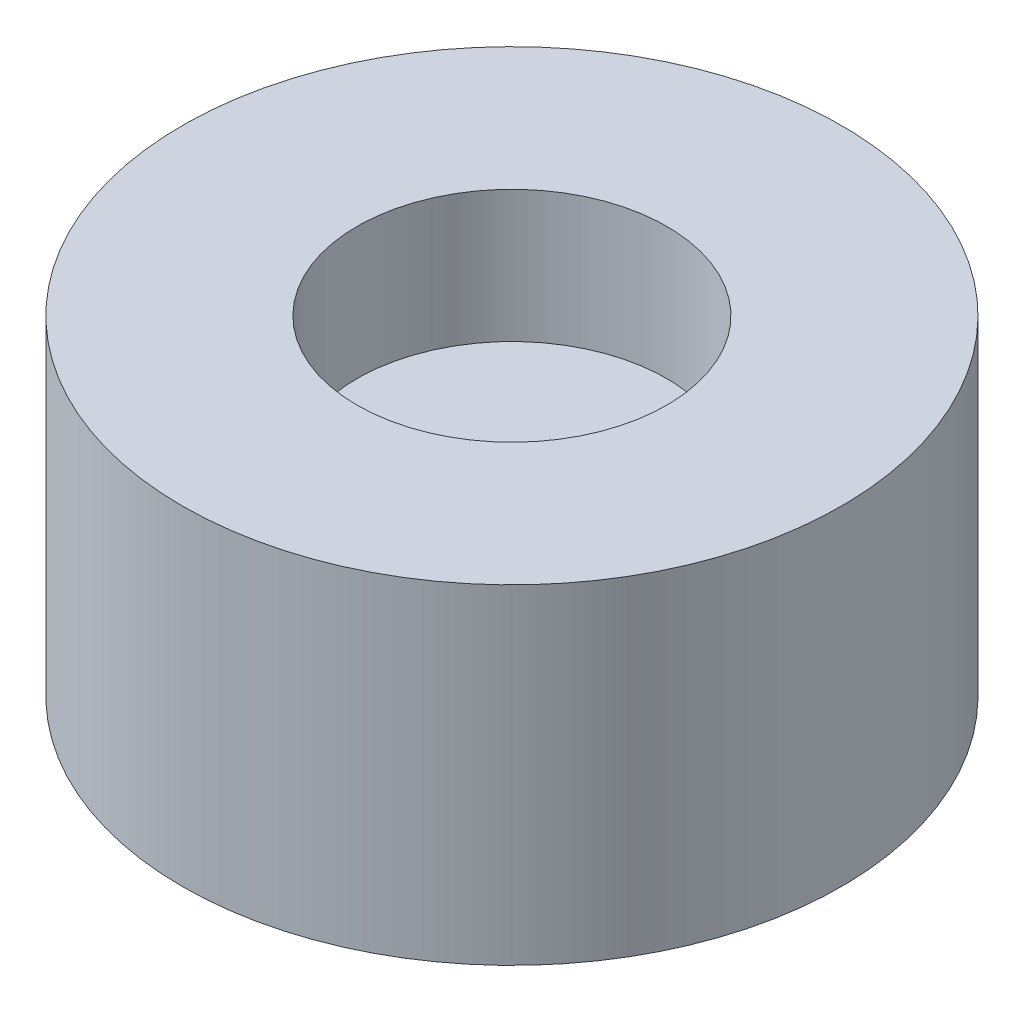
SolidWorks part; units mm, degrees
ref_plane "Front Plane" through (0, 0, 0) normal (0, 0, 1) x (1, 0, 0)
ref_plane "Top Plane" through (0, 0, 0) normal (0, 1, 0) x (1, 0, 0)
ref_plane "Right Plane" through (0, 0, 0) normal (1, 0, 0) x (0, 0, -1)
sketch "Sketch1" plane through (0, 0, 0) normal (0, 1, 0) x (1, 0, 0)
  circle A0 centre (0, 0) radius 12.7
  dimension "D1" = 25.4
extrude "Boss-Extrude1" add sketch "Sketch1" along normal blind 12.7
sketch "Sketch2" plane through (0, 12.7, 0) normal (0, 1, 0) x (1, 0, 0)
  circle A0 centre (0, 0) radius 5.969
  dimension "D1" = 11.938
extrude "Cut-Extrude1" cut sketch "Sketch2" against normal blind 5.08
